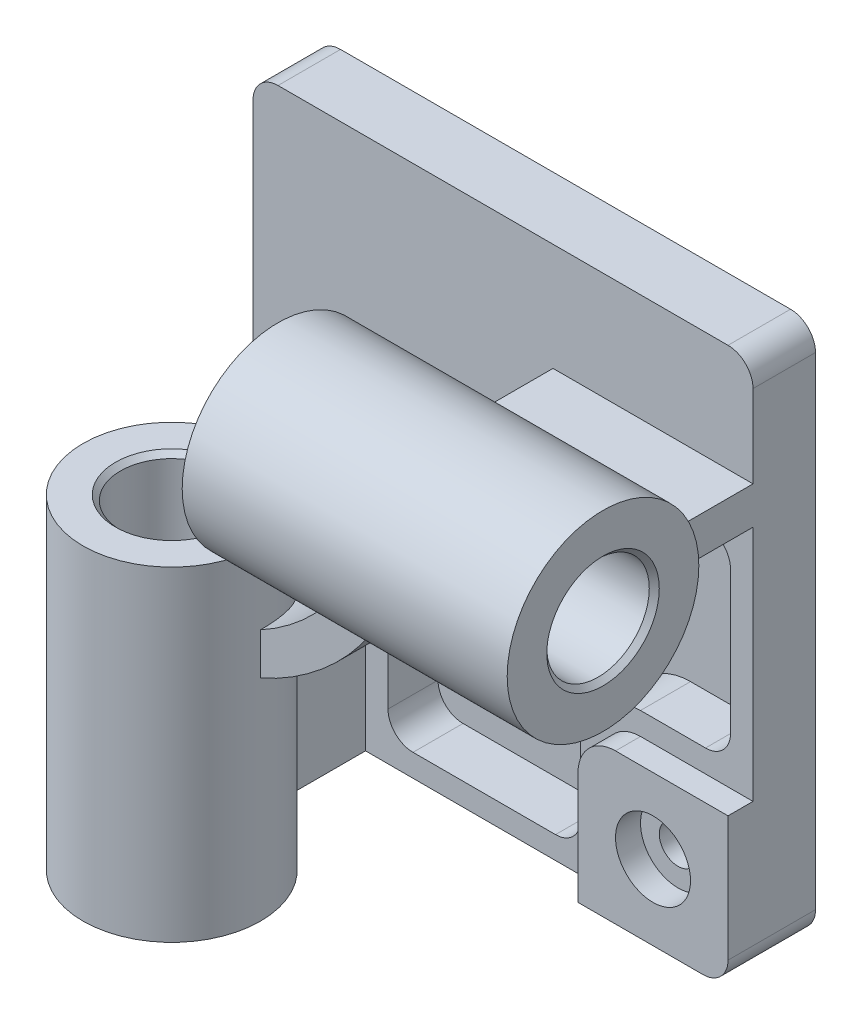
SolidWorks part; units mm, degrees
material "Alloy Steel"
ref_plane "Front Plane" through (0, 0, 0) normal (0, 0, 1) x (1, 0, 0)
ref_plane "Top Plane" through (0, 0, 0) normal (0, 1, 0) x (1, 0, 0)
ref_plane "Right Plane" through (0, 0, 0) normal (1, 0, 0) x (0, 0, -1)
sketch "Sketch1" plane through (0, 0, 0) normal (0, 0, 1) x (1, 0, 0)
  line L1 (10, 0) -> (190, 0)
  line L2 (0, 10) -> (0, 203)
  line L3 (10, 213) -> (190, 213)
  line L4 (200, 10) -> (200, 203)
  arc A0 (10, 0) -> (0, 10) centre (10, 10) cw
  arc A1 (190, 0) -> (200, 10) centre (190, 10) ccw
  arc A2 (190, 213) -> (200, 203) centre (190, 203) cw
  arc A3 (0, 203) -> (10, 213) centre (10, 203) cw
  point P5 (0, 0)
  point P8 (0, 0)
  point P11 (200, 0)
  point P16 (0, 213)
  dimension "D3" = 10
  dimension "D1" = 213
  dimension "D2" = 200
extrude "Boss-Extrude1" add sketch "Sketch1" along normal blind 25
sketch "Sketch2" plane through (0, 0, 25) normal (0, 0, 1) x (1, 0, 0)
  line L0 (200, 60) -> (200, 10)
  line L1 (200, 10) -> (200, 203) construction
  line L2 (190, 0) -> (140, 0)
  line L3 (10, 0) -> (190, 0) construction
  line L4 (140, 0) -> (140, 45)
  line L5 (155, 60) -> (200, 60)
  arc A0 (200, 10) -> (190, 0) centre (190, 10) cw
  arc A1 (140, 45) -> (155, 60) centre (155, 45) cw
  dimension "D1" = 15
  dimension "D2" = 60
  dimension "D3" = 60
extrude "Boss-Extrude2" add sketch "Sketch2" along normal blind 10
hole_wizard "CBORE for M8 Hex Head Bolt1" positions "Sketch3" profile "Sketch4" counterbore size "M8" standard "ANSI Metric" end condition through all
sketch "Sketch3" plane through (0, 0, 35) normal (0, 0, 1) x (1, 0, 0)
  line L0 (140, 0) -> (190, 0) construction
  line L1 (200, 10) -> (200, 60) construction
  point P0 (170, 30)
  dimension "D1" = 30
  dimension "D2" = 30
sketch "Sketch4" plane through (170, 30, 35) normal (1, 0, 0) x (0, -1, 0)
  line L0 (0, 0) -> (0, 35)
  line L1 (0, 35) -> (7.5, 35)
  line L3 (7.5, 35) -> (7.5, 10)
  line L4 (7.5, 10) -> (15, 10)
  line L5 (15, 10) -> (15, 0)
  line L7 (15, 0) -> (0, 0)
  line L11 (0, -6.35) -> (0, 107.95) construction
  dimension "Thru Hole Dia." = 15
  dimension "Thru Hole Depth" = 35
  dimension "C'Bore Dia." = 30
  dimension "C'Bore Depth" = 10
sketch "Sketch5" plane through (0, 0, 25) normal (0, 0, 1) x (1, 0, 0)
  line L0 (30, 0) -> (30, 80)
  line L1 (10, 0) -> (140, 0) construction
  line L2 (120, 170) -> (200, 170)
  line L3 (200, 60) -> (200, 203) construction
  line L4 (45, 0) -> (45, 66.077)
  line L5 (133.923, 155) -> (200, 155)
  line L6 (200, 170) -> (200, 155)
  line L7 (45, 0) -> (30, 0)
  arc A0 (30, 80) -> (120, 170) centre (30, 170) ccw
  arc A1 (45, 66.077) -> (133.923, 155) centre (30, 170) ccw
  dimension "D2" = 80
  dimension "D3" = 170
  dimension "D1" = 80
  dimension "D4" = 15
extrude "Boss-Extrude3" add sketch "Sketch5" along normal blind 70
sketch "Sketch6" plane through (0, 0, 25) normal (0, 0, 1) x (1, 0, 0)
  line L0 (54, 50.7524) -> (54, 19)
  line L1 (64, 9) -> (121, 9)
  line L2 (131, 19) -> (131, 45)
  line L3 (155, 69) -> (181, 69)
  line L4 (191, 79) -> (191, 136)
  line L5 (181, 146) -> (149.2476, 146)
  line L6 (45, 66.077) -> (45, 0)
  line L7 (45, 0) -> (140, 0)
  line L8 (140, 0) -> (140, 45)
  line L9 (155, 60) -> (200, 60)
  line L10 (200, 60) -> (200, 155)
  line L11 (200, 155) -> (133.923, 155)
  line L12 (45, 66.077) -> (45, 0)
  line L13 (45, 0) -> (140, 0)
  line L14 (140, 0) -> (140, 45)
  line L15 (155, 60) -> (200, 60)
  line L16 (200, 60) -> (200, 155)
  line L18 (200, 155) -> (133.923, 155) construction
  line L19 (54, 58.5549) -> (54, 9) construction
  line L20 (54, 9) -> (131, 9) construction
  line L21 (131, 9) -> (131, 45) construction
  line L22 (155, 69) -> (191, 69) construction
  line L23 (191, 69) -> (191, 146) construction
  line L24 (191, 146) -> (141.4451, 146) construction
  arc A0 (155, 69) -> (131, 45) centre (155, 45) ccw
  arc A1 (61.2581, 60.3691) -> (139.6309, 138.7419) centre (30, 170) ccw
  arc A2 (155, 60) -> (140, 45) centre (155, 45) ccw
  arc A3 (45, 66.077) -> (133.923, 155) centre (30, 170) ccw
  arc A4 (155, 60) -> (140, 45) centre (155, 45) ccw
  arc A5 (45, 66.077) -> (133.923, 155) centre (30, 170) ccw
  arc A6 (54, 58.5549) -> (141.4451, 146) centre (30, 170) ccw construction
  arc A7 (54, 50.7524) -> (61.2581, 60.3691) centre (64, 50.7524) cw
  arc A8 (54, 19) -> (64, 9) centre (64, 19) ccw
  arc A9 (121, 9) -> (131, 19) centre (121, 19) ccw
  arc A10 (181, 69) -> (191, 79) centre (181, 79) ccw
  arc A11 (191, 136) -> (181, 146) centre (181, 136) ccw
  arc A12 (149.2476, 146) -> (139.6309, 138.7419) centre (149.2476, 136) ccw
  dimension "D3" = 10
  dimension "D1" = 0
  dimension "D2" = 9
extrude "Cut-Extrude1" cut sketch "Sketch6" against normal offset from surface (20 mm away) 5 contours A11 L5 A12 A1 A7 L0 A8 L1 A9 L2 A0 L3 A10 L4 up to face at (177.5, 30, 0)
ref_plane "Plane1" through (0, -10, 0) normal (0, -1, 0) x (-1, 0, 0)
sketch "Sketch7" plane through (0, -10, 0) normal (0, -1, 0) x (-1, 0, 0)
  line L0 (-10, 0) -> (-190, 0) construction
  line L1 (-30, -95) -> (-30, -25) construction
  circle A0 centre (-37.5, -95) radius 35.5
  point P2 (0, 0)
  dimension "D1" = 71
  dimension "D2" = 95
  dimension "D3" = 7.5
extrude "Boss-Extrude4" add sketch "Sketch7" against normal blind 130
sketch "Sketch8" plane through (0, -10, 0) normal (0, -1, 0) x (1, 0, 0)
  circle A0 centre (37.5, 95) radius 20.5
  circle A1 centre (37.5, 95) radius 35.5 construction
  dimension "D1" = 41
extrude "Cut-Extrude2" cut sketch "Sketch8" against normal through all
ref_plane "Plane2" through (210, 0, 0) normal (1, 0, 0) x (0, 0, -1)
sketch "Sketch9" plane through (210, 0, 0) normal (1, 0, 0) x (0, 0, -1)
  line L0 (-95, 155) -> (-95, 170) construction
  circle A0 centre (-95, 162.5) radius 38.3333
  point P4 (0, 0)
  dimension "D1" = 76.6667
extrude "Boss-Extrude5" add sketch "Sketch9" against normal blind 130
sketch "Sketch10" plane through (210, 0, 0) normal (1, 0, 0) x (0, 0, -1)
  circle A0 centre (-95, 162.5) radius 20.5
  circle A1 centre (-95, 162.5) radius 38.3333 construction
  dimension "D1" = 41
extrude "Cut-Extrude3" cut sketch "Sketch10" against normal through all
chamfer "Chamfer1" distance 2 angle 45 4 edges at (80, 162.5, 74.5) (37.5, 120, 74.5) (37.5, -10, 74.5) (210, 162.5, 74.5)
equation "\"A\"=213"
equation "\"D1@Sketch1\"=\"A\""
equation "\"B\"=200"
equation "\"D2@Sketch1\"=\"B\""
equation "\"C\"= 170"
equation "\"D\"= 130"
equation "\"E\"= 41"
equation "\"X\"= \"A\" / 3"
equation "\"Y\"= \"B\" / 3 + 10"
equation "\"D3@Sketch5\"=\"C\""
equation "\"D1@Sketch7\"=\"X\""
equation "\"D1@Boss-Extrude4\"=\"D\""
equation "\"D1@Sketch8\"=\"E\""
equation "\"D1@Sketch9\"=\"Y\""
equation "\"D1@Boss-Extrude5\"=\"D\""
equation "\"D1@Sketch10\"=\"E\""
